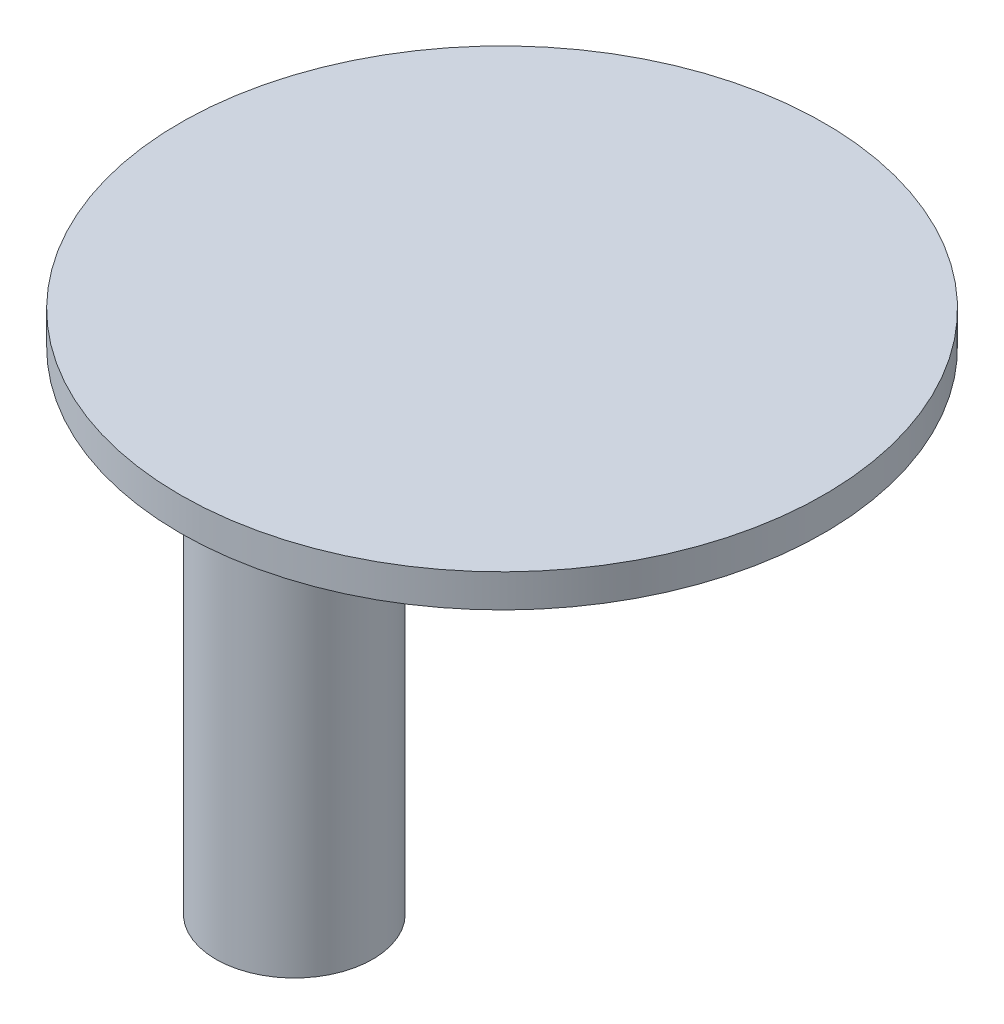
SolidWorks part; units mm, degrees
ref_plane "Front Plane" through (0, 0, 0) normal (0, 0, 1) x (1, 0, 0)
ref_plane "Top Plane" through (0, 0, 0) normal (0, 1, 0) x (1, 0, 0)
ref_plane "Right Plane" through (0, 0, 0) normal (1, 0, 0) x (0, 0, -1)
sketch "Sketch1" plane through (0, 0, 0) normal (0, 1, 0) x (1, 0, 0)
  circle A0 centre (0, 0) radius 4.75
  dimension "D1" = 9.5
extrude "Boss-Extrude1" add sketch "Sketch1" along normal blind 32
sketch "Sketch2" plane through (0, 0, 0) normal (0, -1, 0) x (1, 0, 0)
  circle A0 centre (0, 0) radius 1.8
  dimension "D1" = 3.6
extrude "Cut-Extrude1" cut sketch "Sketch2" against normal blind 3
sketch "Sketch3" plane through (0, 32, 0) normal (0, 1, 0) x (1, 0, 0)
  circle A0 centre (8.56, 4.02) radius 19.5
  circle A1 centre (0, 0) radius 4.75 construction
  point P5 (-23.7749, 8.9429)
  dimension "D3" = 39
  dimension "D1" = 4.02
  dimension "D2" = 8.56
extrude "Boss-Extrude2" add sketch "Sketch3" along normal blind 2
